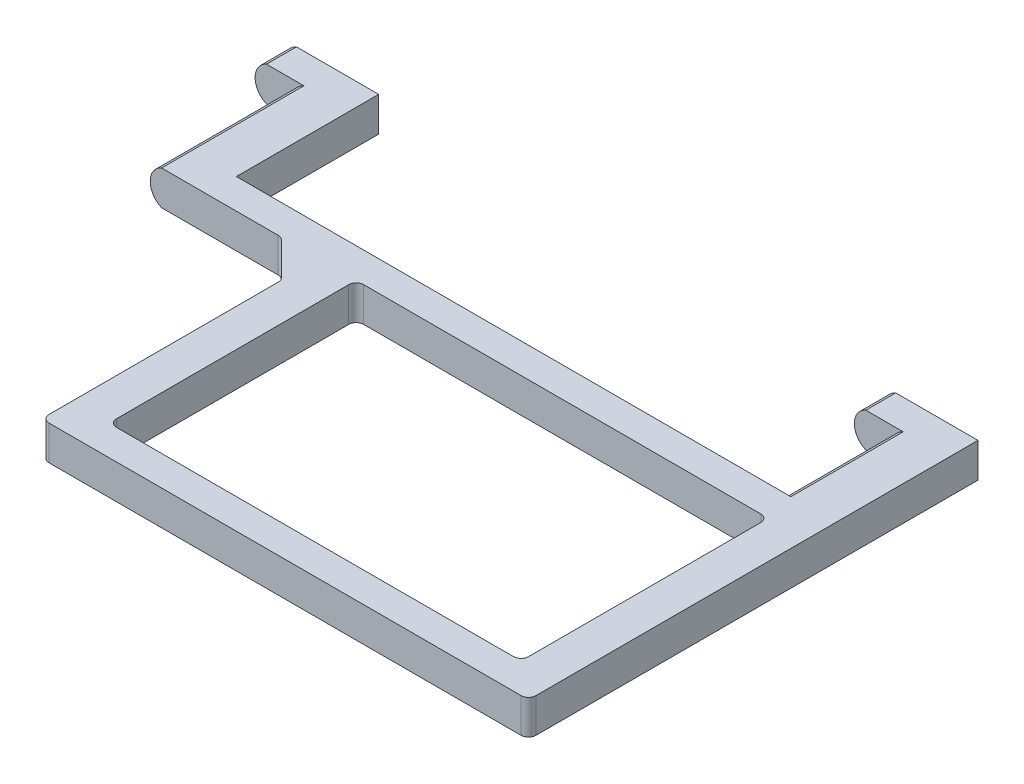
SolidWorks part; units mm, degrees
ref_plane "前视基准面" through (0, 0, 0) normal (0, 0, 1) x (1, 0, 0)
ref_plane "上视基准面" through (0, 0, 0) normal (0, 1, 0) x (1, 0, 0)
ref_plane "右视基准面" through (0, 0, 0) normal (1, 0, 0) x (0, 0, -1)
other "Configuration Table"
sketch "草图1" plane through (0, 0, 0) normal (0, 0, 1) x (1, 0, 0)
  line L2 (544.3012, 447.7441) -> (534.3012, 447.7441) construction
  line L3 (544.3012, 452.7441) -> (534.3012, 452.7441) construction
  line L6 (544.3012, 447.7441) -> (534.3012, 447.7441) construction
  line L7 (544.3012, 452.7441) -> (534.3012, 452.7441) construction
  line L8 (539.3012, 452.7441) -> (539.3012, 447.7441)
  line L9 (539.3012, 452.7441) -> (534.3012, 452.7441)
  line L10 (539.3012, 447.7441) -> (534.3012, 447.7441)
  line L18 (464.3012, 447.7441) -> (454.3012, 447.7441) construction
  line L19 (464.3012, 452.7441) -> (454.3012, 452.7441) construction
  line L20 (464.3012, 447.7441) -> (454.3012, 447.7441) construction
  line L21 (464.3012, 452.7441) -> (454.3012, 452.7441) construction
  line L28 (459.3012, 452.7441) -> (459.3012, 447.7441)
  line L29 (459.3012, 447.7441) -> (454.3012, 447.7441)
  line L30 (454.3012, 452.7441) -> (459.3012, 452.7441)
  arc A2 (534.3012, 452.7441) -> (534.3012, 447.7441) centre (534.3012, 450.2441) ccw construction
  arc A3 (544.3012, 447.7441) -> (544.3012, 452.7441) centre (544.3012, 450.2441) ccw construction
  arc A6 (534.3012, 452.7441) -> (534.3012, 447.7441) centre (534.3012, 450.2441) ccw
  arc A7 (544.3012, 447.7441) -> (544.3012, 452.7441) centre (544.3012, 450.2441) ccw construction
  arc A12 (454.3012, 452.7441) -> (454.3012, 447.7441) centre (454.3012, 450.2441) ccw construction
  arc A13 (454.3012, 452.7441) -> (454.3012, 447.7441) centre (454.3012, 450.2441) ccw
extrude "凸台-拉伸1" add sketch "草图1" against normal up to surface (15 mm away)
sketch "草图2" plane through (0, 0, -15) normal (0, 0, -1) x (-1, 0, 0)
  line L0 (-529.3012, 452.7441) -> (-534.3012, 452.7441)
  line L1 (-529.3012, 447.7441) -> (-534.3012, 447.7441)
  line L2 (-449.3012, 452.7441) -> (-459.3012, 452.7441)
  line L3 (-534.3012, 452.7441) -> (-539.3012, 452.7441)
  line L4 (-539.3012, 452.7441) -> (-539.3012, 447.7441)
  line L5 (-539.3012, 447.7441) -> (-534.3012, 447.7441)
  line L6 (-534.3012, 452.7441) -> (-539.3012, 452.7441)
  line L7 (-539.3012, 452.7441) -> (-539.3012, 447.7441)
  line L8 (-539.3012, 447.7441) -> (-534.3012, 447.7441)
  line L9 (-449.3012, 447.7441) -> (-459.3012, 447.7441)
  line L10 (-464.3012, 447.7441) -> (-454.3012, 447.7441) construction
  line L11 (-459.3012, 452.7441) -> (-459.3012, 447.7441)
  arc A0 (-529.3012, 447.7441) -> (-529.3012, 452.7441) centre (-529.3012, 450.2441) ccw
  arc A1 (-534.3012, 447.7441) -> (-534.3012, 452.7441) centre (-534.3012, 450.2441) ccw
  arc A2 (-534.3012, 447.7441) -> (-534.3012, 452.7441) centre (-534.3012, 450.2441) ccw construction
  arc A3 (-454.3012, 447.7441) -> (-454.3012, 452.7441) centre (-454.3012, 450.2441) ccw construction
  arc A4 (-454.3012, 447.7441) -> (-454.3012, 452.7441) centre (-454.3012, 450.2441) ccw construction
  arc A5 (-449.3012, 447.7441) -> (-449.3012, 452.7441) centre (-449.3012, 450.2441) ccw
  dimension "D1" = 0
extrude "凸台-拉伸2" add sketch "草图2" along normal blind 4
sketch "草图7" plane through (0, 0, 0) normal (0, 0, 1) x (1, 0, 0)
  line L0 (539.3012, 447.7441) -> (454.3012, 447.7441)
  line L1 (544.3012, 447.7441) -> (534.3012, 447.7441) construction
  line L2 (539.3012, 452.7441) -> (454.3012, 452.7441)
  line L3 (539.3012, 452.7441) -> (539.3012, 447.7441)
  arc A0 (454.3012, 452.7441) -> (454.3012, 447.7441) centre (454.3012, 450.2441) ccw construction
  arc A1 (454.3012, 452.7441) -> (454.3012, 447.7441) centre (454.3012, 450.2441) ccw
extrude "凸台-拉伸5" add sketch "草图7" along normal blind 4
sketch "草图8" plane through (0, 0, 4) normal (0, 0, 1) x (1, 0, 0)
  line L0 (539.3012, 452.7441) -> (539.3012, 447.7441)
  line L1 (539.3012, 447.7441) -> (534.3012, 447.7441)
  line L2 (454.3012, 447.7441) -> (539.3012, 447.7441) construction
  line L3 (534.3012, 447.7441) -> (534.3012, 452.7441)
  line L4 (539.3012, 452.7441) -> (454.3012, 452.7441) construction
  line L5 (534.3012, 452.7441) -> (539.3012, 452.7441)
  line L6 (479.3012, 452.7441) -> (479.3012, 447.7441)
  line L7 (479.3012, 447.7441) -> (474.3012, 447.7441)
  line L8 (474.3012, 447.7441) -> (474.3012, 452.7441)
  line L9 (474.3012, 452.7441) -> (479.3012, 452.7441)
  dimension "D1" = 5
  dimension "D2" = 5
  dimension "D3" = 55
extrude "凸台-拉伸6" add sketch "草图8" along normal blind 37
sketch "草图9" plane through (534.3012, 0, 0) normal (-1, 0, 0) x (0, 0, 1)
  line L1 (41, 452.7441) -> (41, 447.7441)
  line L2 (41, 447.7441) -> (37, 447.7441)
  line L3 (41, 447.7441) -> (4, 447.7441) construction
  line L4 (37, 447.7441) -> (37, 452.7441)
  line L5 (41, 452.7441) -> (4, 452.7441) construction
  line L6 (37, 452.7441) -> (41, 452.7441)
  dimension "D1" = 4
extrude "凸台-拉伸7" add sketch "草图9" along normal up to surface (60 mm away) up to face at (474.3012, 450.2441, 22.5)
sketch "草图10" plane through (0, 447.7441, 0) normal (0, -1, 0) x (1, 0, 0)
  line L0 (474.3012, 4) -> (469.3012, 4)
  line L1 (454.3012, 4) -> (474.3012, 4) construction
  line L2 (469.3012, 4) -> (474.3012, 9)
  line L3 (474.3012, 41) -> (474.3012, 4) construction
  line L4 (474.3012, 9) -> (474.3012, 4)
  dimension "D1" = 5
  dimension "D2" = 5
extrude "凸台-拉伸8" add sketch "草图10" against normal up to surface (5 mm away) up to face at (506.8012, 452.7441, 20.5)
fillet "圆角1" radius 1 4 edges at (534.3012, 450.2441, 37) (479.3012, 450.2441, 37) (534.3012, 450.2441, 4) (479.3012, 450.2441, 4)
fillet "圆角2" radius 1 4 edges at (469.3012, 450.2441, 4) (474.3012, 450.2441, 9) (539.3012, 450.2441, 41) (474.3012, 450.2441, 41)
sketch "草图11" plane through (0, 0, 41) normal (0, 0, 1) x (1, 0, 0)
  line L0 (538.3012, 452.7441) -> (475.3012, 452.7441) construction
  line L1 (540.5877, 452.7441) -> (446.1797, 452.7441)
  line L2 (540.5877, 452.7441) -> (540.5877, 452.5441)
  line L3 (540.5877, 452.5441) -> (446.1797, 452.5441)
  line L4 (446.1797, 452.7441) -> (446.1797, 452.5441)
  line L5 (475.3012, 447.7441) -> (538.3012, 447.7441) construction
  line L6 (540.5877, 447.7441) -> (446.1797, 447.7441)
  line L7 (540.5877, 447.7441) -> (540.5877, 447.9441)
  line L8 (540.5877, 447.9441) -> (446.1797, 447.9441)
  line L9 (446.1797, 447.7441) -> (446.1797, 447.9441)
  dimension "D1" = 0.2
  dimension "D2" = 0.2
extrude "切除-拉伸1" cut sketch "草图11" against normal through all
